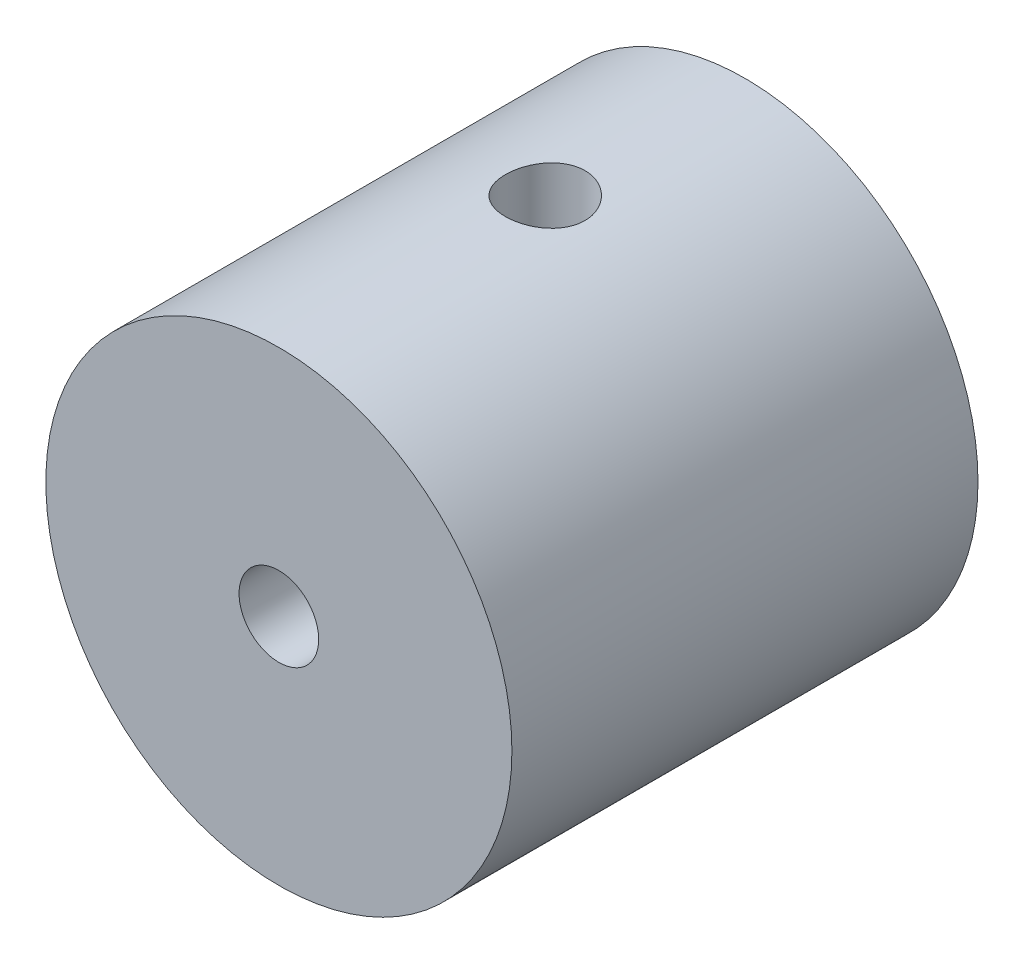
SolidWorks part; units mm, degrees
ref_plane "Front Plane" through (0, 0, 0) normal (0, 0, 1) x (1, 0, 0)
ref_plane "Top Plane" through (0, 0, 0) normal (0, 1, 0) x (1, 0, 0)
ref_plane "Right Plane" through (0, 0, 0) normal (1, 0, 0) x (0, 0, -1)
sketch "Sketch2" plane through (0, 0, 0) normal (0, 0, 1) x (1, 0, 0)
  circle A0 centre (0, 0) radius 11.1125
  dimension "D1" = 22.225
extrude "Boss-Extrude1" add sketch "Sketch2" against normal blind 22.225
hole_wizard "#10-24 Tapped Hole1" positions "Sketch3" profile "Sketch4" tap size "#10-24" standard "ANSI Inch" end condition through all
sketch "Sketch3" plane through (0, 0, 0) normal (0, 0, 1) x (1, 0, 0)
  point P0 (0, 0)
sketch "Sketch4" plane through (0, 0, 0) normal (1, 0, 0) x (0, -1, 0)
  line L0 (0, 0) -> (0, 22.225)
  line L1 (0, 22.225) -> (1.8986, 22.225)
  line L2 (1.8986, 22.225) -> (1.8986, 0)
  line L5 (1.8986, 0) -> (0, 0)
  line L11 (0, -6.35) -> (0, 107.95) construction
  dimension "Thru Tap Drill Dia." = 3.7973
  dimension "Thru Tap Drill Depth" = 22.225
cosmetic thread "Hole Thread1" parameters "D2"=4.826
sketch "Sketch5" plane through (0, 0, 0) normal (0, 1, 0) x (1, 0, 0)
  line L0 (0, 0) -> (0, 12.7) construction
  dimension "D1" = 12.7
hole_wizard "#10-24 Tapped Hole2" positions "Sketch6" profile "Sketch7" tap size "#10-24" standard "ANSI Inch"
sketch "Sketch6" plane through (0, 0, 0) normal (0, 1, 0) x (1, 0, 0)
  point P0 (0, 12.7)
sketch "Sketch7" plane through (0, 0, -12.7) normal (1, 0, 0) x (0, 0, -1)
  line L0 (0, 0) -> (0, 11.1125)
  line L1 (0, 11.1125) -> (1.8986, 11.1125)
  line L2 (1.8986, 11.1125) -> (1.8986, 0)
  line L5 (1.8986, 0) -> (0, 0)
  line L11 (0, -6.35) -> (0, 107.95) construction
  dimension "Thru Tap Drill Dia." = 3.7973
  dimension "Thru Tap Drill Depth" = 11.1125
cosmetic thread "Hole Thread2" parameters "D2"=4.826
hole_wizard "#10-24 Tapped Hole3" positions "Sketch8" profile "Sketch9" tap size "#10-24" standard "ANSI Inch" end condition through all
sketch "Sketch8" plane through (0, 0, 0) normal (0, 1, 0) x (1, 0, 0)
  point P0 (0, 12.7)
sketch "Sketch9" plane through (0, 0, -12.7) normal (1, 0, 0) x (0, 0, 1)
  line L0 (0, 0) -> (0, 11.1125)
  line L1 (0, 11.1125) -> (1.8986, 11.1125)
  line L2 (1.8986, 11.1125) -> (1.8986, 0)
  line L5 (1.8986, 0) -> (0, 0)
  line L11 (0, -6.35) -> (0, 107.95) construction
  dimension "Thru Tap Drill Dia." = 3.7973
  dimension "Thru Tap Drill Depth" = 11.1125
cosmetic thread "Hole Thread3" parameters "D2"=4.826
